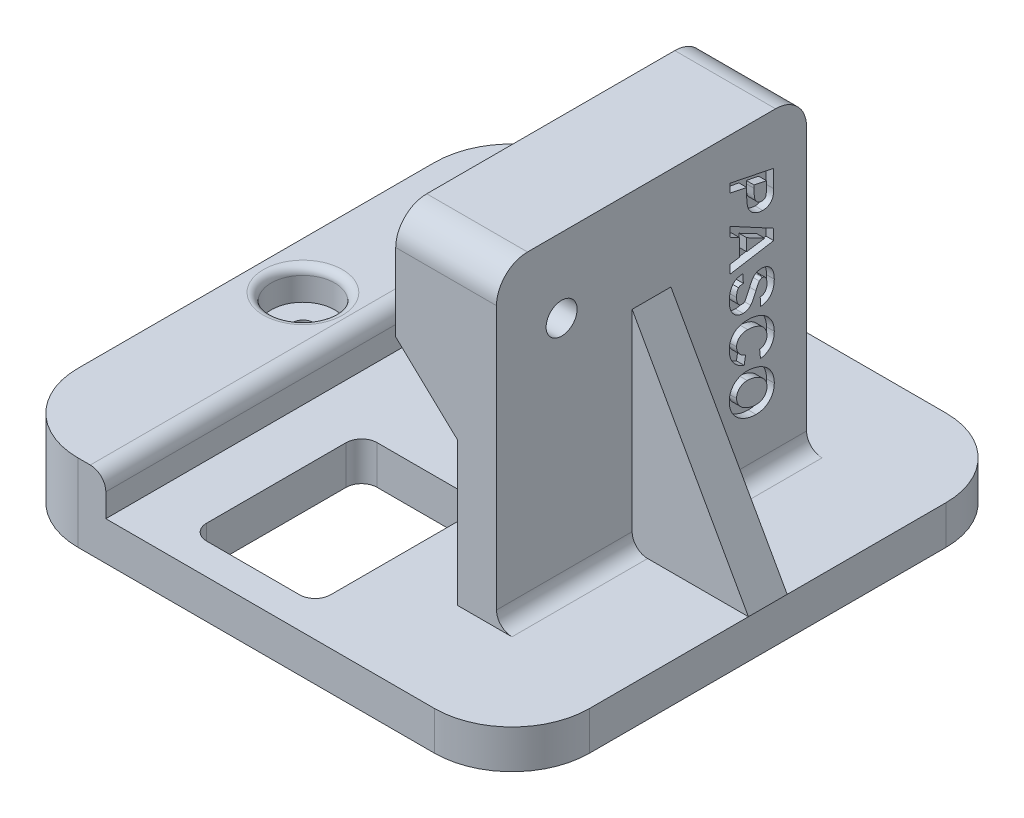
SolidWorks part; units mm, degrees
ref_plane "Front Plane" through (0, 0, 0) normal (0, 0, 1) x (1, 0, 0)
ref_plane "Top Plane" through (0, 0, 0) normal (0, 1, 0) x (1, 0, 0)
ref_plane "Right Plane" through (0, 0, 0) normal (1, 0, 0) x (0, 0, -1)
sketch "Sketch1" plane through (0, 0, 0) normal (0, 1, 0) x (1, 0, 0)
  line L1 (-41.91, 41.91) -> (41.91, 41.91)
  line L2 (-41.91, 41.91) -> (-41.91, -41.91)
  line L3 (-41.91, -41.91) -> (41.91, -41.91)
  line L4 (41.91, 41.91) -> (41.91, -41.91)
  line L5 (-41.91, 41.91) -> (41.91, -41.91) construction
  line L6 (-41.91, -41.91) -> (41.91, 41.91) construction
  point P0 (0, 0)
  dimension "D1" = 83.82
  dimension "D2" = 83.82
extrude "Boss-Extrude1" add sketch "Sketch1" along normal blind 6.35
sketch "Sketch2" plane through (0, 0, 0) normal (0, 0, 1) x (1, 0, 0)
  line L0 (-41.91, 6.35) -> (41.91, 6.35) construction
  line L1 (22.86, 6.35) -> (16.51, 6.35)
  line L2 (22.86, 6.35) -> (22.86, 57.15)
  line L3 (22.86, 57.15) -> (16.51, 57.15)
  line L4 (16.51, 6.35) -> (16.51, 29.8044)
  line L5 (41.91, 6.35) -> (41.91, 0) construction
  line L6 (16.51, 29.8044) -> (6.35, 39.37)
  line L7 (6.35, 39.37) -> (6.35, 57.15)
  line L8 (6.35, 57.15) -> (16.51, 57.15)
  dimension "D1" = 33.02
  dimension "D2" = 6.35
  dimension "D3" = 50.8
  dimension "D4" = 10.16
  dimension "D5" = 19.05
extrude "Boss-Extrude2" add sketch "Sketch2" along normal mid plane 50.8
sketch "Sketch3" plane through (22.86, 0, 0) normal (1, 0, 0) x (0, 0, -1)
  line L0 (-25.4, 6.35) -> (25.4, 6.35) construction
  line L1 (-25.4, 6.35) -> (-25.4, 57.15) construction
  circle A0 centre (-14.732, 44.958) radius 2.54
  dimension "D2" = 5.08
  dimension "D1" = 38.608
  dimension "D3" = 10.668
extrude "Cut-Extrude1" cut sketch "Sketch3" against normal up to next
sketch "Sketch7" plane through (0, 6.35, 0) normal (0, 1, 0) x (1, 0, 0)
  line L0 (-41.91, -41.91) -> (41.91, -41.91) construction
  line L1 (-41.91, 41.91) -> (-24.638, 41.91)
  line L2 (-41.91, 41.91) -> (-41.91, -41.91)
  line L3 (-41.91, -41.91) -> (-24.638, -41.91)
  line L4 (-24.638, 41.91) -> (-24.638, -41.91)
  line L6 (22.86, -25.4) -> (22.86, 25.4) construction
  point P7 (22.86, 0)
  dimension "D1" = 47.498
extrude "Boss-Extrude3" add sketch "Sketch7" against normal blind 3.81 and the other way blind 6.35
fillet "Fillet1" radius 2.54 1 edges at (-24.638, 12.7, 0)
sketch "Sketch8" plane through (0, 0, 0) normal (0, 0, 1) x (1, 0, 0)
  line L0 (22.86, 40.4401) -> (41.91, 6.35)
  line L1 (22.86, 6.35) -> (22.86, 57.15) construction
  line L2 (-24.638, 6.35) -> (41.91, 6.35) construction
  line L3 (41.91, 6.35) -> (22.86, 6.35)
  line L4 (22.86, 6.35) -> (22.86, 40.4401)
extrude "Boss-Extrude4" add sketch "Sketch8" along normal mid plane 6.35
sketch "Sketch9" plane through (22.86, 0, 0) normal (1, 0, 0) x (0, 0, -1)
  line L0 (12.8271, 50.7819) -> (12.8271, 15.7479) construction
  text T0 "PASCO" font "Arial" height in points 28
extrude "Cut-Extrude3" cut sketch "Sketch9" against normal blind 1.27
fillet "Fillet2" radius 12.7 4 edges at (-41.91, 6.35, 41.91) (-41.91, 6.35, -41.91) (41.91, 3.175, -41.91) (41.91, 3.175, 41.91)
fillet "Fillet3" radius 5.08 2 edges at (14.605, 57.15, -25.4) (14.605, 57.15, 25.4)
sketch "Sketch10" plane through (0, 6.35, 0) normal (0, 1, 0) x (1, 0, 0)
  line L0 (-24.638, 41.91) -> (-24.638, -41.91) construction
  line L1 (-15.748, 36.83) -> (4.572, 36.83)
  line L2 (-15.748, 36.83) -> (-15.748, 8.89)
  line L3 (-15.748, 8.89) -> (4.572, 8.89)
  line L4 (4.572, 36.83) -> (4.572, 8.89)
  line L5 (-15.748, -8.89) -> (4.572, -8.89)
  line L6 (-15.748, -8.89) -> (-15.748, -36.83)
  line L7 (-15.748, -36.83) -> (4.572, -36.83)
  line L8 (4.572, -8.89) -> (4.572, -36.83)
  line L9 (-24.638, -41.91) -> (29.21, -41.91) construction
  line L10 (29.21, 41.91) -> (-24.638, 41.91) construction
  dimension "D1" = 8.89
  dimension "D2" = 8.89
  dimension "D3" = 20.32
  dimension "D4" = 27.94
  dimension "D5" = 5.08
  dimension "D6" = 5.08
extrude "Cut-Extrude4" cut sketch "Sketch10" against normal through all
fillet "Fillet4" radius 2.54 8 edges at (4.572, 3.175, 36.83) (4.572, 3.175, -8.89) (-15.748, 3.175, -8.89) (-15.748, 3.175, 36.83) (-15.748, 3.175, 8.89) (-15.748, 3.175, -36.83) (4.572, 3.175, -36.83) (4.572, 3.175, 8.89)
fillet "Fillet5" radius 2.54 2 edges at (22.86, 6.35, -14.2875) (22.86, 6.35, 14.2875)
sketch "Sketch11" plane through (16.51, 0, 0) normal (-1, 0, 0) x (0, 0, 1)
  line L0 (25.4, 29.8044) -> (-25.4, 29.8044) construction
  line L1 (-25.4, 29.8044) -> (-25.4, 6.35) construction
  circle A0 centre (-10.922, 18.3744) radius 3.81
  dimension "D1" = 7.62
  dimension "D2" = 11.43
  dimension "D3" = 14.478
extrude "Cut-Extrude5" cut sketch "Sketch11" against normal blind 2.54
fillet "Fillet6" radius 0.508 1 edges at (16.51, 18.3744, -7.112)
sketch "Sketch12" plane through (-41.91, 0, 0) normal (-1, 0, 0) x (0, 0, 1)
  text T0 "Cart Balance" font "Arial" height in points 22
extrude "Cut-Extrude6" cut sketch "Sketch12" against normal blind 1.27
sketch "Sketch13" plane through (6.35, 0, 0) normal (-1, 0, 0) x (0, 0, 1)
  circle A0 centre (14.732, 44.958) radius 4.318
  dimension "D1" = 8.636
extrude "Cut-Extrude7" cut sketch "Sketch13" against normal blind 5.08
fillet "Fillet7" radius 0.508 1 edges at (6.35, 40.64, 14.732)
sketch "Sketch14" plane through (0, 12.7, 0) normal (0, 1, 0) x (1, 0, 0)
  circle A0 centre (-34.2497, 0) radius 1.651
  dimension "D1" = 3.302
extrude "Cut-Extrude8" cut sketch "Sketch14" against normal through all
sketch "Sketch15" plane through (0, 12.7, 0) normal (0, 1, 0) x (1, 0, 0)
  circle A0 centre (-34.2497, 0) radius 5.207
  dimension "D1" = 10.414
extrude "Cut-Extrude9" cut sketch "Sketch15" against normal blind 5.08
fillet "Fillet8" radius 1.27 1 edges at (-34.2497, 12.7, 5.207)
